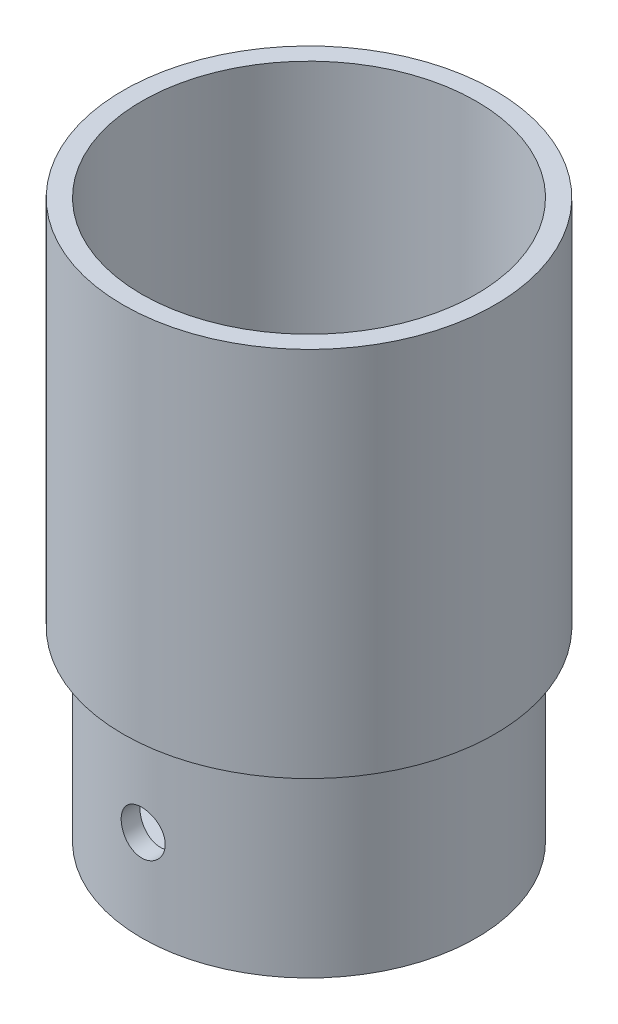
SolidWorks part; units mm, degrees
ref_plane "Alzado" through (0, 0, 0) normal (0, 0, 1) x (1, 0, 0)
ref_plane "Planta" through (0, 0, 0) normal (0, 1, 0) x (1, 0, 0)
ref_plane "Vista lateral" through (0, 0, 0) normal (1, 0, 0) x (0, 0, -1)
sketch "Croquis1" plane through (0, 0, 0) normal (0, 1, 0) x (1, 0, 0)
  circle A0 centre (0, 0) radius 45
extrude "Saliente-Extruir1" add sketch "Croquis1" along normal blind 50
sketch "Croquis2" plane through (0, 50, 0) normal (0, 1, 0) x (1, 0, 0)
  circle A0 centre (0, 0) radius 40
extrude "Cortar-Extruir1" cut sketch "Croquis2" against normal blind 40
sketch "Croquis3" plane through (0, 0, 0) normal (0, -1, 0) x (1, 0, 0)
  circle A0 centre (0, 0) radius 6.5413
extrude "Cortar-Extruir2" cut sketch "Croquis3" against normal blind 40
sketch "Croquis4" plane through (0, 0, 0) normal (0, -1, 0) x (1, 0, 0)
  line L1 (-10.0704, 7.7189) -> (-3.0123, 7.7189)
  line L2 (-10.0704, 7.7189) -> (-10.0704, -7.7189)
  line L3 (-10.0704, -7.7189) -> (-3.0123, -7.7189)
  line L4 (-3.0123, 7.7189) -> (-3.0123, -7.7189)
  line L5 (-10.0704, 7.7189) -> (-3.0123, -7.7189) construction
  line L6 (-10.0704, -7.7189) -> (-3.0123, 7.7189) construction
  circle A0 centre (0, 0) radius 6.5413 construction
  point P0 (-6.5413, 0)
extrude "Saliente-Extruir3" add sketch "Croquis4" against normal blind 10
sketch "Croquis6" plane through (0, 0, 0) normal (0, 0, 1) x (1, 0, 0)
  circle A0 centre (0, 24.5636) radius 5.9217
extrude "Cortar-Extruir4" cut sketch "Croquis6" against normal through all both and the other way through all
sketch "Croquis9" plane through (0, 50, 0) normal (0, 1, 0) x (1, 0, 0)
  circle A0 centre (0, 0) radius 50
extrude "Saliente-Extruir5" add sketch "Croquis9" along normal blind 100
sketch "Croquis10" plane through (0, 150, 0) normal (0, 1, 0) x (1, 0, 0)
  circle A0 centre (0, 0) radius 45
extrude "Cortar-Extruir6" cut sketch "Croquis10" against normal blind 100
